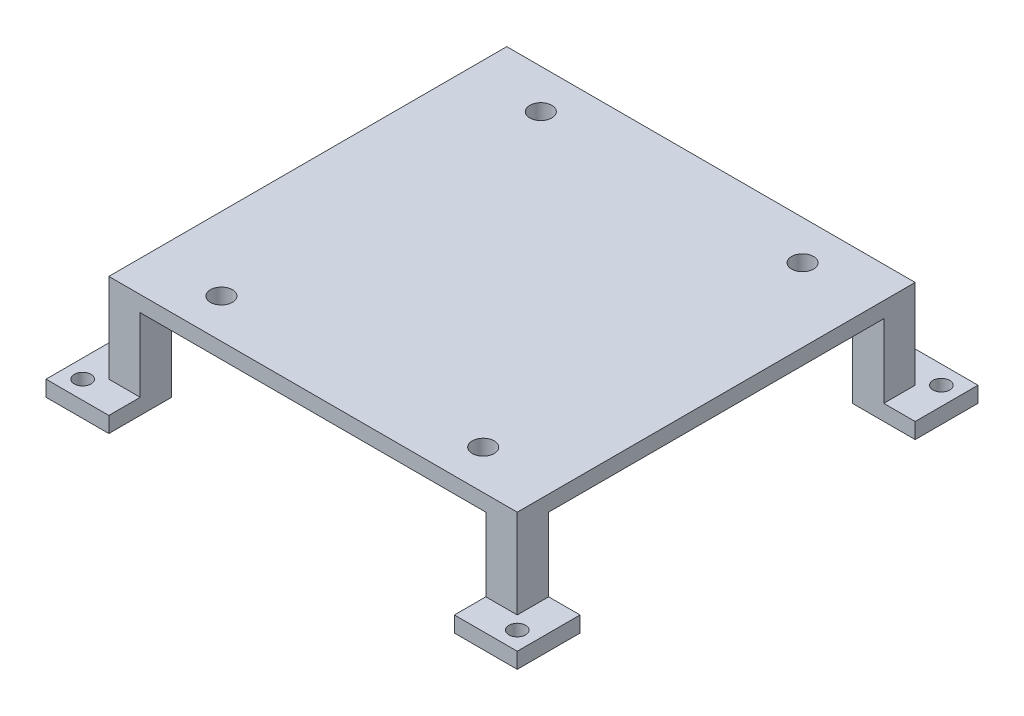
SolidWorks part; units mm, degrees
ref_plane "Front Plane" through (0, 0, 0) normal (0, 0, 1) x (1, 0, 0)
ref_plane "Top Plane" through (0, 0, 0) normal (0, 1, 0) x (1, 0, 0)
ref_plane "Right Plane" through (0, 0, 0) normal (1, 0, 0) x (0, 0, -1)
sketch "Sketch1" plane through (0, 0, 0) normal (0, 1, 0) x (1, 0, 0)
  line L0 (0, 52.7327) -> (0, -52.7327) construction
  line L1 (-69.5376, 0) -> (69.5376, 0) construction
  line L2 (-45, -44) -> (-33, -44)
  line L3 (-45, 44) -> (-33, 44)
  line L4 (-45, 44) -> (-45, 32)
  line L5 (-45, 32) -> (-33, 32)
  line L6 (-33, 44) -> (-33, 32)
  line L7 (-45, -44) -> (-45, -32)
  line L8 (-33, -44) -> (-33, -32)
  line L9 (-45, -32) -> (-33, -32)
  line L10 (45, 44) -> (33, 44)
  line L11 (45, 44) -> (45, 32)
  line L12 (45, 32) -> (33, 32)
  line L13 (33, 44) -> (33, 32)
  line L14 (45, -44) -> (45, -32)
  line L15 (45, -44) -> (33, -44)
  line L16 (33, -44) -> (33, -32)
  line L17 (45, -32) -> (33, -32)
  point P12 (0, 0)
  point P13 (0, 0)
  dimension "D1" = 45
  dimension "D5" = 12
  dimension "D6" = 12
  dimension "D7" = 32
extrude "Boss-Extrude1" add sketch "Sketch1" along normal blind 3
sketch "Sketch2" plane through (0, 3, 0) normal (0, 1, 0) x (1, 0, 0)
  line L0 (-33, 32) -> (-33, 44) construction
  line L1 (-33, 38) -> (-39, 38)
  line L2 (-33, 38) -> (-33, 32)
  line L3 (-33, 32) -> (-39, 32)
  line L4 (-39, 38) -> (-39, 32)
  line L5 (-45, 32) -> (-33, 32) construction
  line L8 (-33, -32) -> (-45, -32) construction
  line L9 (-39, -32) -> (-33, -32)
  line L10 (33, 44) -> (33, 32) construction
  line L11 (33, 38) -> (39, 38)
  line L12 (33, 38) -> (33, 32)
  line L13 (33, 32) -> (39, 32)
  line L14 (-39, -32) -> (-39, -38)
  line L15 (-39, -38) -> (-33, -38)
  line L16 (-33, -32) -> (-33, -38)
  line L17 (-33, -44) -> (-33, -32) construction
  line L18 (39, 38) -> (39, 32)
  line L19 (33, 32) -> (45, 32) construction
  line L20 (33, -32) -> (33, -44) construction
  line L21 (33, -38) -> (39, -38)
  line L22 (33, -38) -> (33, -32)
  line L23 (33, -32) -> (39, -32)
  line L24 (39, -38) -> (39, -32)
  line L25 (45, -32) -> (33, -32) construction
  dimension "D1" = 6
  dimension "D2" = 6
  dimension "D3" = 6
  dimension "D4" = 6
  dimension "D5" = 6
  dimension "D6" = 6
  dimension "D7" = 6
extrude "Boss-Extrude3" add sketch "Sketch2" along normal blind 14
sketch "Sketch3" plane through (0, 17, 0) normal (0, 1, 0) x (1, 0, 0)
  line L1 (-39, 38) -> (39, 38)
  line L2 (-39, 38) -> (-39, -38)
  line L3 (-39, -38) -> (39, -38)
  line L4 (39, 38) -> (39, -38)
extrude "Boss-Extrude4" add sketch "Sketch3" along normal blind 3
sketch "Sketch4" plane through (0, 3, 0) normal (0, 1, 0) x (1, 0, 0)
  line L2 (0, 0) -> (0, 49.386) construction
  line L7 (45, 44) -> (33, 44) construction
  line L8 (45, 32) -> (45, 44) construction
  line L9 (0, 0) -> (72.0946, 0) construction
  circle A0 centre (41.5, -40.5) radius 1.6
  circle A1 centre (-41.5, 40.5) radius 1.6
  circle A2 centre (-41.5, -40.5) radius 1.6
  circle A3 centre (41.5, 40.5) radius 1.6
  dimension "D1" = 3.2
  dimension "D8" = 3.5
  dimension "D9" = 3.5
extrude "Cut-Extrude1" cut sketch "Sketch4" against normal up to next
sketch "Sketch5" plane through (0, 20, 0) normal (0, 1, 0) x (1, 0, 0)
  line L0 (0, 0) -> (0, 49.3257) construction
  line L3 (0, 0) -> (66.453, 0) construction
  circle A0 centre (25, 30.5) radius 2.1
  circle A1 centre (25, -30.5) radius 2.1
  circle A2 centre (-25, 30.5) radius 2.1
  circle A3 centre (-25, -30.5) radius 2.1
  dimension "D1" = 4.2
  dimension "D2" = 50
  dimension "D3" = 61
extrude "Cut-Extrude2" cut sketch "Sketch5" against normal up to next
